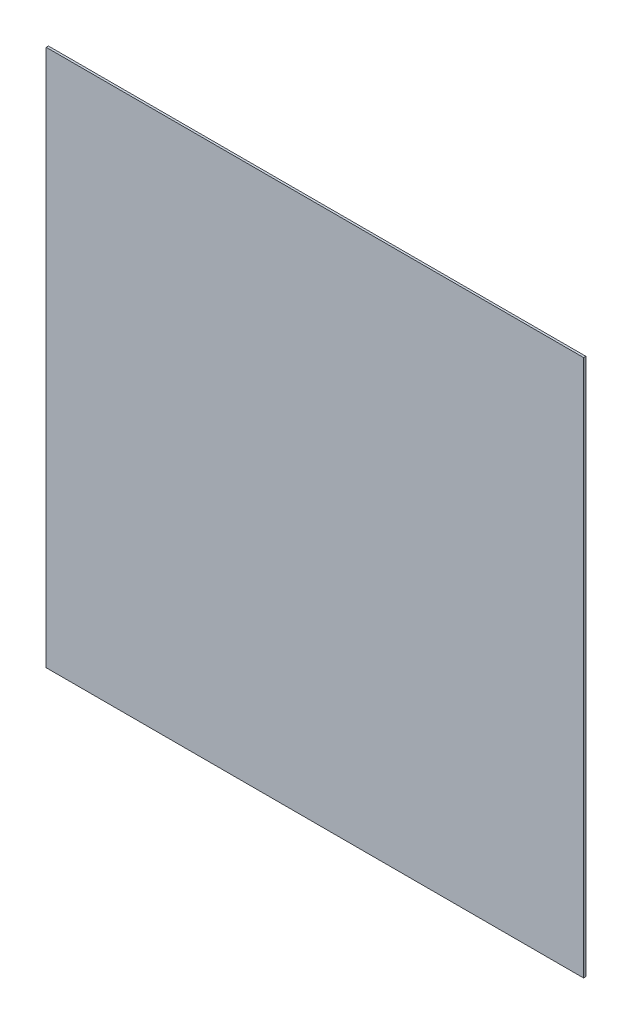
SolidWorks part; units mm, degrees
ref_plane "Front Plane" through (0, 0, 0) normal (0, 0, 1) x (1, 0, 0)
ref_plane "Top Plane" through (0, 0, 0) normal (0, 1, 0) x (1, 0, 0)
ref_plane "Right Plane" through (0, 0, 0) normal (1, 0, 0) x (0, 0, -1)
sketch "Sketch1" plane through (0, 0, 0) normal (0, 0, 1) x (1, 0, 0)
  line L1 (0, 0) -> (762, 0)
  line L2 (0, 0) -> (0, 762)
  line L3 (0, 762) -> (762, 762)
  line L4 (762, 0) -> (762, 762)
  dimension "D1" = 762
extrude "Boss-Extrude1" add sketch "Sketch1" along normal blind 3.175
